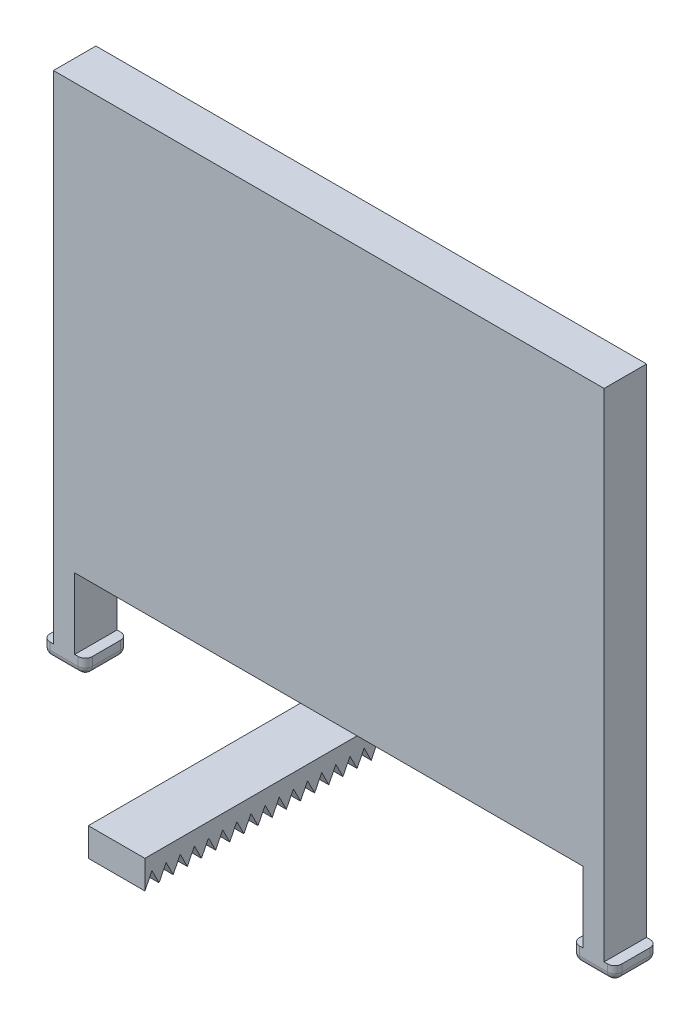
SolidWorks part; units mm, degrees
ref_plane "Ön Düzlem" through (0, 0, 0) normal (0, 0, 1) x (1, 0, 0)
ref_plane "Üst Düzlem" through (0, 0, 0) normal (0, 1, 0) x (1, 0, 0)
ref_plane "Sağ Düzlem" through (0, 0, 0) normal (1, 0, 0) x (0, 0, -1)
sketch "Çizim1" plane through (0, 0, 0) normal (0, 0, 1) x (1, 0, 0)
  line L0 (-19.3708, 54.614) -> (19.5583, 54.614)
  line L1 (19.5583, 54.614) -> (19.5583, 19.5055)
  line L2 (19.5583, 19.5055) -> (20.3083, 19.5055)
  line L3 (20.3083, 19.5055) -> (20.3083, 18.5055)
  line L4 (20.3083, 18.5055) -> (17.3083, 18.5055)
  line L5 (17.3083, 18.5055) -> (17.3083, 19.614)
  line L6 (17.3083, 19.614) -> (18.0583, 19.614)
  line L7 (18.0583, 19.614) -> (18.0583, 24.614)
  line L8 (18.0583, 24.614) -> (-17.8708, 24.614)
  line L9 (-17.8708, 24.614) -> (-17.8708, 19.614)
  line L10 (-17.8708, 19.614) -> (-17.1208, 19.614)
  line L11 (-17.1208, 19.614) -> (-17.1208, 18.5055)
  line L12 (-17.1208, 18.5055) -> (-20.1208, 18.5055)
  line L13 (-20.1208, 18.5055) -> (-20.1208, 19.5055)
  line L14 (-20.1208, 19.5055) -> (-19.3708, 19.5055)
  line L15 (-19.3708, 19.5055) -> (-19.3708, 54.614)
extrude "Yükseklik-Ekstrüzyon1" add sketch "Çizim1" along normal blind 3
sketch "Çizim2" plane through (0, 0, 3) normal (0, 0, 1) x (1, 0, 0)
  line L0 (-17.8708, 24.614) -> (18.0583, 24.614) construction
  line L1 (-1.9058, 24.614) -> (2.0942, 24.614)
  line L2 (-1.9058, 24.614) -> (-1.9058, 22.614)
  line L3 (-1.9058, 22.614) -> (2.0942, 22.614)
  line L4 (2.0942, 24.614) -> (2.0942, 22.614)
  point P6 (0.0942, 24.614)
  dimension "D1" = 2
  dimension "D2" = 4
  dimension "D3" = 17.965
  dimension "D4" = 15.965
extrude "Yükseklik-Ekstrüzyon2" add sketch "Çizim2" along normal mid plane 30
sketch "Çizim3" plane through (2.0942, 0, 0) normal (1, 0, 0) x (0, 0, -1)
  line L1 (10.5, 23.614) -> (10, 22.614)
  line L4 (11.5, 23.614) -> (11, 22.614)
  line L5 (-18, 22.614) -> (12, 22.614) construction
  line L6 (11, 22.614) -> (12, 22.614)
  line L7 (11, 22.614) -> (12, 22.614)
  line L8 (11.5, 23.614) -> (11, 22.614)
  line L9 (11.5, 23.614) -> (12, 22.614)
  line L10 (12, 22.614) -> (11, 22.614)
  line L11 (10.5, 23.614) -> (11, 22.614)
  line L12 (10, 22.614) -> (11, 22.614)
  line L13 (9.5, 23.614) -> (9, 22.614)
  line L14 (9.5, 23.614) -> (10, 22.614)
  line L15 (9, 22.614) -> (10, 22.614)
  line L16 (8.5, 23.614) -> (8, 22.614)
  line L17 (8.5, 23.614) -> (9, 22.614)
  line L18 (8, 22.614) -> (9, 22.614)
  line L19 (7.5, 23.614) -> (7, 22.614)
  line L20 (7.5, 23.614) -> (8, 22.614)
  line L21 (7, 22.614) -> (8, 22.614)
  line L22 (6.5, 23.614) -> (6, 22.614)
  line L23 (6.5, 23.614) -> (7, 22.614)
  line L24 (6, 22.614) -> (7, 22.614)
  line L25 (5.5, 23.614) -> (5, 22.614)
  line L26 (5.5, 23.614) -> (6, 22.614)
  line L27 (5, 22.614) -> (6, 22.614)
  line L28 (4.5, 23.614) -> (4, 22.614)
  line L29 (4.5, 23.614) -> (5, 22.614)
  line L30 (4, 22.614) -> (5, 22.614)
  line L31 (3.5, 23.614) -> (3, 22.614)
  line L32 (3.5, 23.614) -> (4, 22.614)
  line L33 (3, 22.614) -> (4, 22.614)
  line L34 (2.5, 23.614) -> (2, 22.614)
  line L35 (2.5, 23.614) -> (3, 22.614)
  line L36 (2, 22.614) -> (3, 22.614)
  line L37 (1.5, 23.614) -> (1, 22.614)
  line L38 (1.5, 23.614) -> (2, 22.614)
  line L39 (1, 22.614) -> (2, 22.614)
  line L40 (0.5, 23.614) -> (0, 22.614)
  line L41 (0.5, 23.614) -> (1, 22.614)
  line L42 (0, 22.614) -> (1, 22.614)
  line L43 (-0.5, 23.614) -> (-1, 22.614)
  line L44 (-0.5, 23.614) -> (0, 22.614)
  line L45 (-1, 22.614) -> (0, 22.614)
  line L46 (-1.5, 23.614) -> (-2, 22.614)
  line L47 (-1.5, 23.614) -> (-1, 22.614)
  line L48 (-2, 22.614) -> (-1, 22.614)
  line L49 (-2.5, 23.614) -> (-3, 22.614)
  line L50 (-2.5, 23.614) -> (-2, 22.614)
  line L51 (-3, 22.614) -> (-2, 22.614)
  line M11 (-18, 22.614) -> (12, 22.614)
  dimension "D1" = 1
  dimension "D2" = 0.5
  dimension "D3" = 0.5
  dimension "D4" = 15
extrude "Kes-Ekstrüzyon1" cut sketch "Çizim3" against normal blind 15 contours L50 L49 M11 | L47 L46 M11 | L35 L34 M11 | L32 L31 M11 | L29 L28 M11 | L26 L25 M11 | L20 L19 M11 | L17 L16 M11 | L14 L13 M11 | L11 L1 M11 | L9 L4 M11 | L44 L45 L43 | L41 L42 L40 | L38 L39 L37 | L23 L24 L22
sketch "Çizim4" plane through (2.0942, 0, 0) normal (1, 0, 0) x (0, 0, -1)
  line L0 (1.5, 23.614) -> (2, 22.614)
  line L1 (2, 22.614) -> (1, 22.614)
  line L2 (1, 22.614) -> (1.5, 23.614)
  line L3 (0, 22.614) -> (0.5, 23.614)
  line L4 (0.5, 23.614) -> (1, 22.614)
  line L5 (1, 22.614) -> (0, 22.614)
  line L6 (-1, 22.614) -> (-0.5, 23.614)
  line L7 (-0.5, 23.614) -> (0, 22.614)
  line L8 (0, 22.614) -> (-1, 22.614)
  line L9 (-2, 22.614) -> (-1.5, 23.614)
  line L10 (-1.5, 23.614) -> (-1, 22.614)
  line L11 (-1, 22.614) -> (-2, 22.614)
  line L12 (-3, 22.614) -> (-2.5, 23.614)
  line L13 (-2.5, 23.614) -> (-2, 22.614)
  line L14 (-2, 22.614) -> (-3, 22.614)
  line L15 (-4, 22.614) -> (-3.5, 23.614)
  line L16 (-3.5, 23.614) -> (-3, 22.614)
  line L17 (-3, 22.614) -> (-4, 22.614)
  line L18 (-5, 22.614) -> (-4.5, 23.614)
  line L19 (-4.5, 23.614) -> (-4, 22.614)
  line L20 (-4, 22.614) -> (-5, 22.614)
  line L21 (-6, 22.614) -> (-5.5, 23.614)
  line L22 (-5.5, 23.614) -> (-5, 22.614)
  line L23 (-5, 22.614) -> (-6, 22.614)
  line L24 (-7, 22.614) -> (-6.5, 23.614)
  line L25 (-6.5, 23.614) -> (-6, 22.614)
  line L26 (-6, 22.614) -> (-7, 22.614)
  line L27 (-8, 22.614) -> (-7.5, 23.614)
  line L28 (-7.5, 23.614) -> (-7, 22.614)
  line L29 (-7, 22.614) -> (-8, 22.614)
  line L30 (-9, 22.614) -> (-8.5, 23.614)
  line L31 (-8.5, 23.614) -> (-8, 22.614)
  line L32 (-8, 22.614) -> (-9, 22.614)
  line L33 (-10, 22.614) -> (-9.5, 23.614)
  line L34 (-9.5, 23.614) -> (-9, 22.614)
  line L35 (-9, 22.614) -> (-10, 22.614)
  line L36 (-11, 22.614) -> (-10.5, 23.614)
  line L37 (-10.5, 23.614) -> (-10, 22.614)
  line L38 (-10, 22.614) -> (-11, 22.614)
  line L39 (-12, 22.614) -> (-11.5, 23.614)
  line L40 (-11.5, 23.614) -> (-11, 22.614)
  line L41 (-11, 22.614) -> (-12, 22.614)
  line L42 (-13, 22.614) -> (-12.5, 23.614)
  line L43 (-12.5, 23.614) -> (-12, 22.614)
  line L44 (-12, 22.614) -> (-13, 22.614)
  line L45 (-14, 22.614) -> (-13.5, 23.614)
  line L46 (-13.5, 23.614) -> (-13, 22.614)
  line L47 (-13, 22.614) -> (-14, 22.614)
  line L48 (-15, 22.614) -> (-14.5, 23.614)
  line L49 (-14.5, 23.614) -> (-14, 22.614)
  line L50 (-14, 22.614) -> (-15, 22.614)
  line L51 (-16, 22.614) -> (-15.5, 23.614)
  line L52 (-15.5, 23.614) -> (-15, 22.614)
  line L53 (-15, 22.614) -> (-16, 22.614)
  line L54 (-17, 22.614) -> (-16.5, 23.614)
  line L55 (-16.5, 23.614) -> (-16, 22.614)
  line L56 (-16, 22.614) -> (-17, 22.614)
  line L57 (-18, 22.614) -> (-17.5, 23.614)
  line L58 (-17.5, 23.614) -> (-17, 22.614)
  line L59 (-17, 22.614) -> (-18, 22.614)
  line M32 (-18, 22.614) -> (-3, 22.614)
  dimension "D1" = 20
extrude "Kes-Ekstrüzyon2" cut sketch "Çizim4" against normal blind 10 contours L37 L36 M32 | L31 L30 M32 | L59 L57 L58 | L56 L54 L55 | L53 L51 L52 | L50 L48 L49 | L47 L45 L46 | L44 L42 L43 | L40 L41 L39 | L35 L33 L34 | L29 L27 L28 | L26 L24 L25 | L23 L21 L22 | L20 L18 L19 | L17 L15 L16 | L14 L12 L13 | L9 L10 L11 | L8 L6 L7 | L5 L3 L4
fillet "Radyus5" radius 0.5 2 edges at (18.8083, 18.5055, 0) (18.8083, 18.5055, 3)
fillet "Radyus6" radius 0.5 2 edges at (-18.6208, 18.5055, 0) (-18.6208, 18.5055, 3)
fillet "Radyus7" radius 0.5 10 edges at (-20.1208, 19.2555, 0) (-20.1208, 18.652, 0.1464) (-20.1208, 18.5055, 1.5) (-20.1208, 18.652, 2.8536) (-17.1208, 19.3098, 0) (-17.1208, 18.652, 0.1464) (-17.1208, 18.5055, 1.5) (-17.1208, 18.652, 2.8536) (-20.1208, 19.2555, 3) (-17.1208, 19.3098, 3)
fillet "Radyus8" radius 0.5 10 edges at (17.3083, 19.3098, 0) (17.3083, 18.652, 0.1464) (17.3083, 18.5055, 1.5) (17.3083, 18.652, 2.8536) (20.3083, 19.2555, 0) (20.3083, 18.652, 0.1464) (20.3083, 18.5055, 1.5) (20.3083, 18.652, 2.8536) (17.3083, 19.3098, 3) (20.3083, 19.2555, 3)
